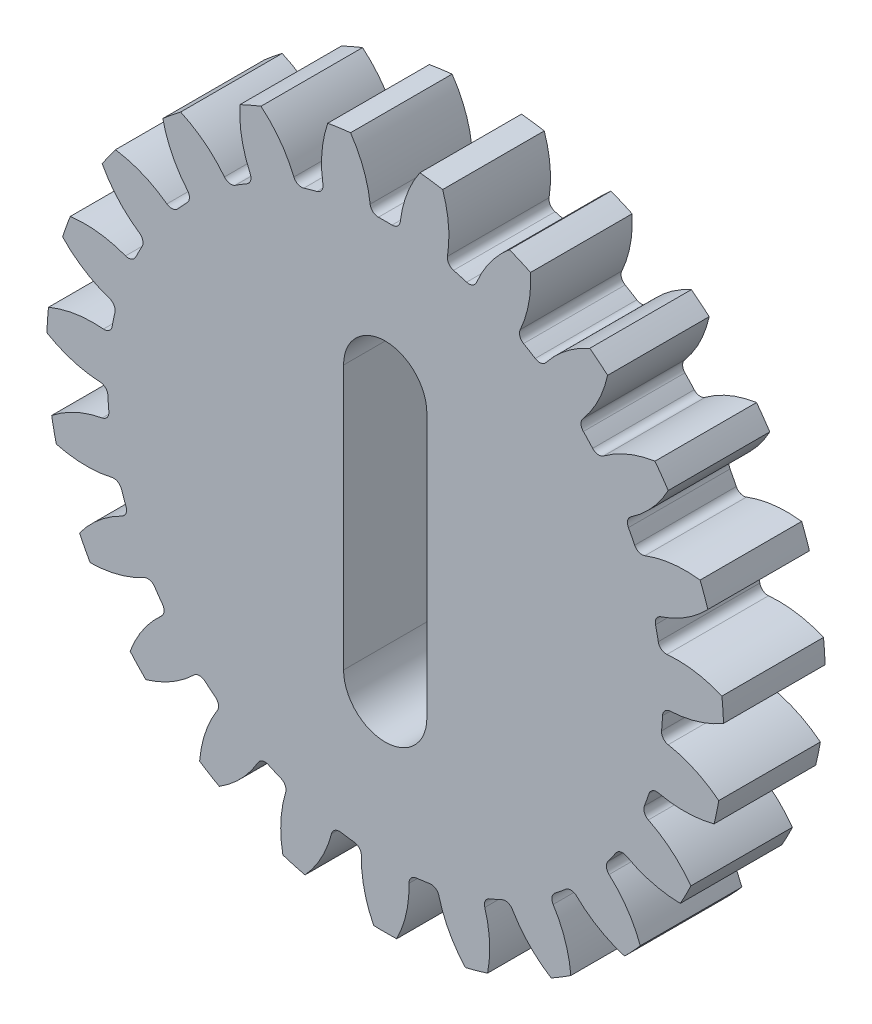
SolidWorks part; units mm, degrees
material "1023 Carbon Steel Sheet (SS)"
ref_plane "Front Plane" through (0, 0, 0) normal (0, 0, 1) x (1, 0, 0)
ref_plane "Top Plane" through (0, 0, 0) normal (0, 1, 0) x (1, 0, 0)
ref_plane "Right Plane" through (0, 0, 0) normal (1, 0, 0) x (0, 0, -1)
sketch "skBase" plane through (0, 0, 0) normal (0, 0, 1) x (1, 0, 0)
  circle A0 centre (0, 0) radius 15.3295
  circle A1 centre (0, 0) radius 16.6625
  circle A2 centre (0, 0) radius 13.6632
  dimension "D1" = 30.659
  dimension "D2" = 1.333
  dimension "D3" = 2.9992
extrude "Base" add sketch "skBase" along normal mid plane 5 contours A1
sketch "skToothProfile" plane through (0, 0, 0) normal (0, 0, 1) x (1, 0, 0)
  line L0 (0, 0) -> (0, 16.6625) construction
  line L1 (-1.0461, 15.2938) -> (1.0461, 15.2938) construction
  line L2 (-0.7109, 13.6447) -> (0, 0) construction
  line L3 (0, 12.4196) -> (-1.8721, 17.563) construction
  line L4 (0, 0) -> (2.2689, 16.5073) construction
  line L5 (1.0461, 15.2938) -> (3.1189, 15.0089) construction
  circle A0 centre (0, 0) radius 16.6625 construction
  arc A1 (-0.7109, 13.6447) -> (-2.4887, 17.4863) centre (-6.3896, 13.3489) ccw
  arc A2 (0.7109, 13.6447) -> (2.4887, 17.4863) centre (6.3896, 13.3489) cw
  circle A3 centre (0, 0) radius 13.6632 construction
  arc A4 (0.7109, 13.6447) -> (-0.7109, 13.6447) centre (0, 0) ccw
  circle A5 centre (0, 0) radius 15.3295 construction
  circle A6 centre (0, 0) radius 16.6625 construction
  circle A7 centre (0, 0) radius 17.6625
  arc A8 (2.4887, 17.4863) -> (-2.4887, 17.4863) centre (0, 0) ccw
  dimension "D2" = 20
  dimension "D3" = 7.826
  dimension "D1" = 1
extrude "ToothProfile" cut sketch "skToothProfile" against normal through all and the other way through all
fillet "FilletToothProfile" radius 0.3999 2 edges at (0.7109, 13.6447, 0) (-0.7109, 13.6447, 0)
fillet "Fillet1" [suppressed] radius 0.75
pattern_circular "CirPatternTeeth" count 23 over 360 about axis through (0, 0, 0) along (0, 0, 1) of "ToothProfile", "FilletToothProfile", "Fillet1"
sketch "skChaveta" plane through (0, 0, 2.5) normal (0, 0, 1) x (1, 0, 0)
  line L0 (0, 1.25) -> (0, 0) construction
  circle A0 centre (0, 0) radius 1.25
  dimension "D1" = 2.5
sketch "skRebaixo" plane through (0, 0, 2.5) normal (0, 0, 1) x (1, 0, 0)
  circle A0 centre (0, 0) radius 21.5
  circle A1 centre (0, 0) radius 7.5
  dimension "D1" = 43
  dimension "D2" = 15
sketch "Sketch4" plane through (0, 0, -2.5) normal (0, 0, -1) x (-1, 0, 0)
  circle A0 centre (0, 0) radius 17.5
  arc A2 (0.335, 13.6591) -> (-0.335, 13.6591) centre (0, 0) ccw
  arc A3 (0.335, 13.6591) -> (-0.335, 13.6591) centre (0, 0) ccw
  arc A63 (-1.7068, 16.5749) -> (-2.8283, 16.4207) centre (0, 0) ccw
  arc A64 (-1.7068, 16.5749) -> (-2.8283, 16.4207) centre (0, 0) ccw
  arc A67 (3.9479, -16.1881) -> (5.0379, -15.8826) centre (0, 0) ccw
  arc A68 (3.9479, -16.1881) -> (5.0379, -15.8826) centre (0, 0) ccw
  arc A69 (8.1689, -14.5226) -> (9.1362, -13.9344) centre (0, 0) ccw
  arc A70 (8.1689, -14.5226) -> (9.1362, -13.9344) centre (0, 0) ccw
  arc A71 (11.7842, -11.7802) -> (12.5569, -10.9528) centre (0, 0) ccw
  arc A72 (11.7842, -11.7802) -> (12.5569, -10.9528) centre (0, 0) ccw
  arc A73 (14.5254, -8.164) -> (15.0463, -7.1588) centre (0, 0) ccw
  arc A74 (14.5254, -8.164) -> (15.0463, -7.1588) centre (0, 0) ccw
  arc A75 (16.1894, -3.9423) -> (16.4197, -2.8339) centre (0, 0) ccw
  arc A76 (16.1894, -3.9423) -> (16.4197, -2.8339) centre (0, 0) ccw
  arc A77 (16.6527, 0.5717) -> (16.5754, 1.7011) centre (0, 0) ccw
  arc A78 (16.6527, 0.5717) -> (16.5754, 1.7011) centre (0, 0) ccw
  arc A79 (15.8809, 5.0434) -> (15.5018, 6.1101) centre (0, 0) ccw
  arc A80 (15.8809, 5.0434) -> (15.5018, 6.1101) centre (0, 0) ccw
  arc A81 (13.9313, 9.141) -> (13.2785, 10.0658) centre (0, 0) ccw
  arc A82 (13.9313, 9.141) -> (13.2785, 10.0658) centre (0, 0) ccw
  arc A83 (9.1362, -13.9344) -> (8.2674, -11.3378) centre (3.4678, -14.3873) ccw
  arc A84 (9.1362, -13.9344) -> (8.2674, -11.3378) centre (3.4678, -14.3873) ccw
  arc A85 (8.3602, -10.807) -> (8.2674, -11.3378) centre (8.6049, -11.1233) ccw
  arc A86 (8.3602, -10.807) -> (8.2674, -11.3378) centre (8.6049, -11.1233) ccw
  arc A87 (8.3602, -10.807) -> (8.88, -10.3841) centre (0, 0) ccw
  arc A88 (8.3602, -10.807) -> (8.88, -10.3841) centre (0, 0) ccw
  arc A89 (9.4186, -10.4012) -> (8.88, -10.3841) centre (9.1399, -10.688) ccw
  arc A90 (9.4186, -10.4012) -> (8.88, -10.3841) centre (9.1399, -10.688) ccw
  arc A91 (9.4186, -10.4012) -> (11.7842, -11.7802) centre (13.3808, -6.3225) ccw
  arc A92 (9.4186, -10.4012) -> (11.7842, -11.7802) centre (13.3808, -6.3225) ccw
  arc A93 (12.5569, -10.9528) -> (11.0197, -8.6868) centre (7.2209, -12.9182) ccw
  arc A94 (12.5569, -10.9528) -> (11.0197, -8.6868) centre (7.2209, -12.9182) ccw
  arc A95 (10.9659, -8.1507) -> (11.0197, -8.6868) centre (11.2868, -8.3892) ccw
  arc A96 (10.9659, -8.1507) -> (11.0197, -8.6868) centre (11.2868, -8.3892) ccw
  arc A97 (10.9659, -8.1507) -> (11.3523, -7.6032) centre (0, 0) ccw
  arc A98 (10.9659, -8.1507) -> (11.3523, -7.6032) centre (0, 0) ccw
  arc A99 (11.8755, -7.4744) -> (11.3523, -7.6032) centre (11.6846, -7.8258) ccw
  arc A100 (11.8755, -7.4744) -> (11.3523, -7.6032) centre (11.6846, -7.8258) ccw
  arc A101 (11.8755, -7.4744) -> (14.5254, -8.164) centre (14.5904, -2.4779) ccw
  arc A102 (11.8755, -7.4744) -> (14.5254, -8.164) centre (14.5904, -2.4779) ccw
  arc A103 (15.0463, -7.1588) -> (12.9547, -5.3916) centre (10.4384, -10.491) ccw
  arc A104 (15.0463, -7.1588) -> (12.9547, -5.3916) centre (10.4384, -10.491) ccw
  arc A105 (12.7583, -4.8899) -> (12.9547, -5.3916) centre (13.1317, -5.033) ccw
  arc A106 (12.7583, -4.8899) -> (12.9547, -5.3916) centre (13.1317, -5.033) ccw
  arc A107 (12.7583, -4.8899) -> (12.9827, -4.2585) centre (0, 0) ccw
  arc A108 (12.7583, -4.8899) -> (12.9827, -4.2585) centre (0, 0) ccw
  arc A109 (13.4517, -3.9933) -> (12.9827, -4.2585) centre (13.3627, -4.3831) ccw
  arc A110 (13.4517, -3.9933) -> (12.9827, -4.2585) centre (13.3627, -4.3831) ccw
  arc A111 (13.4517, -3.9933) -> (16.1894, -3.9423) centre (14.7179, 1.5504) ccw
  arc A112 (13.4517, -3.9933) -> (16.1894, -3.9423) centre (14.7179, 1.5504) ccw
  arc A113 (16.4197, -2.8339) -> (13.929, -1.6965) centre (12.8817, -7.2857) ccw
  arc A114 (16.4197, -2.8339) -> (13.929, -1.6965) centre (12.8817, -7.2857) ccw
  arc A115 (13.6044, -1.2664) -> (13.929, -1.6965) centre (14.0026, -1.3035) ccw
  arc A116 (13.6044, -1.2664) -> (13.929, -1.6965) centre (14.0026, -1.3035) ccw
  arc A117 (13.6044, -1.2664) -> (13.6502, -0.5979) centre (0, 0) ccw
  arc A118 (13.6044, -1.2664) -> (13.6502, -0.5979) centre (0, 0) ccw
  arc A119 (14.0302, -0.2159) -> (13.6502, -0.5979) centre (14.0497, -0.6154) ccw
  arc A120 (14.0302, -0.2159) -> (13.6502, -0.5979) centre (14.0497, -0.6154) ccw
  arc A121 (14.0302, -0.2159) -> (16.6527, 0.5717) centre (13.7538, 5.4638) ccw
  arc A122 (14.0302, -0.2159) -> (16.6527, 0.5717) centre (13.7538, 5.4638) ccw
  arc A123 (16.5754, 1.7011) -> (13.8702, 2.1244) centre (14.3697, -3.5401) ccw
  arc A124 (16.5754, 1.7011) -> (13.8702, 2.1244) centre (14.3697, -3.5401) ccw
  arc A125 (13.4416, 2.451) -> (13.8702, 2.1244) centre (13.835, 2.5227) ccw
  arc A126 (13.4416, 2.451) -> (13.8702, 2.1244) centre (13.835, 2.5227) ccw
  arc A127 (13.4416, 2.451) -> (13.3053, 3.1071) centre (0, 0) ccw
  arc A128 (13.4416, 2.451) -> (13.3053, 3.1071) centre (0, 0) ccw
  arc A129 (13.5682, 3.5774) -> (13.3053, 3.1071) centre (13.6947, 3.198) ccw
  arc A130 (13.5682, 3.5774) -> (13.3053, 3.1071) centre (13.6947, 3.198) ccw
  arc A131 (13.5682, 3.5774) -> (15.8809, 5.0434) centre (11.7697, 8.9719) ccw
  arc A132 (13.5682, 3.5774) -> (15.8809, 5.0434) centre (11.7697, 8.9719) ccw
  arc A133 (15.5018, 6.1101) -> (12.7827, 5.7877) centre (14.7919, 0.4681) ccw
  arc A134 (15.5018, 6.1101) -> (12.7827, 5.7877) centre (14.7919, 0.4681) ccw
  arc A135 (12.2819, 5.9866) -> (12.7827, 5.7877) centre (12.6414, 6.1618) ccw
  arc A136 (12.2819, 5.9866) -> (12.7827, 5.7877) centre (12.6414, 6.1618) ccw
  arc A137 (12.2819, 5.9866) -> (11.9736, 6.5816) centre (0, 0) ccw
  arc A138 (12.2819, 5.9866) -> (11.9736, 6.5816) centre (0, 0) ccw
  arc A139 (12.0999, 7.1054) -> (11.9736, 6.5816) centre (12.3241, 6.7742) ccw
  arc A140 (12.0999, 7.1054) -> (11.9736, 6.5816) centre (12.3241, 6.7742) ccw
  arc A141 (12.0999, 7.1054) -> (13.9313, 9.141) centre (8.9126, 11.8146) ccw
  arc A142 (12.0999, 7.1054) -> (13.9313, 9.141) centre (8.9126, 11.8146) ccw
  arc A143 (13.2785, 10.0658) -> (10.7471, 9.0218) centre (14.1171, 4.4415) ccw
  arc A144 (13.2785, 10.0658) -> (10.7471, 9.0218) centre (14.1171, 4.4415) ccw
  arc A145 (10.2113, 9.0782) -> (10.7471, 9.0218) centre (10.5101, 9.3439) ccw
  arc A146 (10.2113, 9.0782) -> (10.7471, 9.0218) centre (10.5101, 9.3439) ccw
  arc A147 (10.2113, 9.0782) -> (9.7539, 9.5679) centre (0, 0) ccw
  arc A148 (10.2113, 9.0782) -> (9.7539, 9.5679) centre (0, 0) ccw
  arc A149 (9.7342, 10.1064) -> (9.7539, 9.5679) centre (10.0394, 9.848) ccw
  arc A150 (9.7342, 10.1064) -> (9.7539, 9.5679) centre (10.0394, 9.848) ccw
  arc A151 (9.7342, 10.1064) -> (10.9485, 12.5606) centre (5.3946, 13.7811) ccw
  arc A152 (9.7342, 10.1064) -> (10.9485, 12.5606) centre (5.3946, 13.7811) ccw
  arc A153 (10.0704, 13.275) -> (7.9145, 11.5868) centre (12.3953, 8.0856) ccw
  arc A154 (10.0704, 13.275) -> (7.9145, 11.5868) centre (12.3953, 8.0856) ccw
  arc A155 (7.3833, 11.4966) -> (7.9145, 11.5868) centre (7.5994, 11.833) ccw
  arc A156 (7.3833, 11.4966) -> (7.9145, 11.5868) centre (7.5994, 11.833) ccw
  arc A157 (7.3833, 11.4966) -> (6.8108, 11.8447) centre (0, 0) ccw
  arc A158 (7.3833, 11.4966) -> (6.8108, 11.8447) centre (0, 0) ccw
  arc A159 (6.6466, 12.3579) -> (6.8108, 11.8447) centre (7.0101, 12.1914) ccw
  arc A160 (6.6466, 12.3579) -> (6.8108, 11.8447) centre (7.0101, 12.1914) ccw
  arc A161 (6.6466, 12.3579) -> (7.1537, 15.0487) centre (1.4764, 14.7255) ccw
  arc A162 (6.6466, 12.3579) -> (7.1537, 15.0487) centre (1.4764, 14.7255) ccw
  arc A163 (6.1154, 15.4997) -> (4.495, 13.2925) centre (9.7542, 11.13) ccw
  arc A164 (6.1154, 15.4997) -> (4.495, 13.2925) centre (9.7542, 11.13) ccw
  arc A165 (4.0078, 13.0622) -> (4.495, 13.2925) centre (4.1251, 13.4445) ccw
  arc A166 (4.0078, 13.0622) -> (4.495, 13.2925) centre (4.1251, 13.4445) ccw
  arc A167 (4.0078, 13.0622) -> (3.3626, 13.243) centre (0, 0) ccw
  arc A168 (4.0078, 13.0622) -> (3.3626, 13.243) centre (0, 0) ccw
  arc A169 (3.066, 13.6928) -> (3.3626, 13.243) centre (3.461, 13.6306) ccw
  arc A170 (3.066, 13.6928) -> (3.3626, 13.243) centre (3.461, 13.6306) ccw
  arc A171 (3.066, 13.6928) -> (2.8283, 16.4207) centre (-2.5512, 14.5778) ccw
  arc A172 (3.066, 13.6928) -> (2.8283, 16.4207) centre (-2.5512, 14.5778) ccw
  arc A173 (1.7068, 16.5749) -> (0.742, 14.0123) centre (6.3896, 13.3489) ccw
  arc A174 (1.7068, 16.5749) -> (0.742, 14.0123) centre (6.3896, 13.3489) ccw
  arc A175 (0.335, 13.6591) -> (0.742, 14.0123) centre (0.3448, 14.0589) ccw
  arc A176 (0.335, 13.6591) -> (0.742, 14.0123) centre (0.3448, 14.0589) ccw
  arc A177 (-0.742, 14.0123) -> (-0.335, 13.6591) centre (-0.3448, 14.0589) ccw
  arc A178 (-0.742, 14.0123) -> (-0.335, 13.6591) centre (-0.3448, 14.0589) ccw
  arc A179 (-0.742, 14.0123) -> (-1.7068, 16.5749) centre (-6.3896, 13.3489) ccw
  arc A180 (-0.742, 14.0123) -> (-1.7068, 16.5749) centre (-6.3896, 13.3489) ccw
  arc A199 (10.9485, 12.5606) -> (10.0704, 13.275) centre (0, 0) ccw
  arc A200 (10.9485, 12.5606) -> (10.0704, 13.275) centre (0, 0) ccw
  arc A201 (7.1537, 15.0487) -> (6.1154, 15.4997) centre (0, 0) ccw
  arc A202 (7.1537, 15.0487) -> (6.1154, 15.4997) centre (0, 0) ccw
  arc A203 (2.8283, 16.4207) -> (1.7068, 16.5749) centre (0, 0) ccw
  arc A204 (2.8283, 16.4207) -> (1.7068, 16.5749) centre (0, 0) ccw
  arc A215 (-9.1362, -13.9344) -> (-8.1689, -14.5226) centre (0, 0) ccw
  arc A216 (-9.1362, -13.9344) -> (-8.1689, -14.5226) centre (0, 0) ccw
  arc A217 (-5.0379, -15.8826) -> (-3.9479, -16.1881) centre (0, 0) ccw
  arc A218 (-5.0379, -15.8826) -> (-3.9479, -16.1881) centre (0, 0) ccw
  arc A219 (-0.566, -16.6529) -> (0.566, -16.6529) centre (0, 0) ccw
  arc A220 (-0.566, -16.6529) -> (0.566, -16.6529) centre (0, 0) ccw
  arc A221 (-1.1729, -13.9828) -> (-0.566, -16.6529) centre (4.5125, -14.0946) ccw
  arc A222 (-1.1729, -13.9828) -> (-0.566, -16.6529) centre (4.5125, -14.0946) ccw
  arc A223 (-3.9479, -16.1881) -> (-2.6431, -13.7807) centre (-8.1478, -12.3545) ccw
  arc A224 (-3.9479, -16.1881) -> (-2.6431, -13.7807) centre (-8.1478, -12.3545) ccw
  arc A225 (-2.1918, -13.4863) -> (-2.6431, -13.7807) centre (-2.256, -13.881) ccw
  arc A226 (-2.1918, -13.4863) -> (-2.6431, -13.7807) centre (-2.256, -13.881) ccw
  arc A227 (-2.1918, -13.4863) -> (-1.528, -13.5775) centre (0, 0) ccw
  arc A228 (-2.1918, -13.4863) -> (-1.528, -13.5775) centre (0, 0) ccw
  arc A229 (-1.1729, -13.9828) -> (-1.528, -13.5775) centre (-1.5727, -13.9749) ccw
  arc A230 (-1.1729, -13.9828) -> (-1.528, -13.5775) centre (-1.5727, -13.9749) ccw
  arc A231 (-11.7842, -11.7802) -> (-9.4186, -10.4012) centre (-13.3808, -6.3225) ccw
  arc A232 (-11.7842, -11.7802) -> (-9.4186, -10.4012) centre (-13.3808, -6.3225) ccw
  arc A233 (-8.88, -10.3841) -> (-9.4186, -10.4012) centre (-9.1399, -10.688) ccw
  arc A234 (-8.88, -10.3841) -> (-9.4186, -10.4012) centre (-9.1399, -10.688) ccw
  arc A235 (-8.88, -10.3841) -> (-8.3602, -10.807) centre (0, 0) ccw
  arc A236 (-8.88, -10.3841) -> (-8.3602, -10.807) centre (0, 0) ccw
  arc A237 (-8.2674, -11.3378) -> (-8.3602, -10.807) centre (-8.6049, -11.1233) ccw
  arc A238 (-8.2674, -11.3378) -> (-8.3602, -10.807) centre (-8.6049, -11.1233) ccw
  arc A239 (-8.2674, -11.3378) -> (-9.1362, -13.9344) centre (-3.4678, -14.3873) ccw
  arc A240 (-8.2674, -11.3378) -> (-9.1362, -13.9344) centre (-3.4678, -14.3873) ccw
  arc A241 (-8.1689, -14.5226) -> (-6.2631, -12.5566) centre (-11.1789, -9.6981) ccw
  arc A242 (-8.1689, -14.5226) -> (-6.2631, -12.5566) centre (-11.1789, -9.6981) ccw
  arc A243 (-5.7491, -12.3948) -> (-6.2631, -12.5566) centre (-5.9174, -12.7576) ccw
  arc A244 (-5.7491, -12.3948) -> (-6.2631, -12.5566) centre (-5.9174, -12.7576) ccw
  arc A245 (-5.7491, -12.3948) -> (-5.1345, -12.6618) centre (0, 0) ccw
  arc A246 (-5.7491, -12.3948) -> (-5.1345, -12.6618) centre (0, 0) ccw
  arc A247 (-4.9019, -13.1478) -> (-5.1345, -12.6618) centre (-5.2848, -13.0324) ccw
  arc A248 (-4.9019, -13.1478) -> (-5.1345, -12.6618) centre (-5.2848, -13.0324) ccw
  arc A249 (-4.9019, -13.1478) -> (-5.0379, -15.8826) centre (0.5424, -14.7894) ccw
  arc A250 (-4.9019, -13.1478) -> (-5.0379, -15.8826) centre (0.5424, -14.7894) ccw
  arc A273 (0.566, -16.6529) -> (1.1729, -13.9828) centre (-4.5125, -14.0946) ccw
  arc A274 (0.566, -16.6529) -> (1.1729, -13.9828) centre (-4.5125, -14.0946) ccw
  arc A275 (1.528, -13.5775) -> (1.1729, -13.9828) centre (1.5727, -13.9749) ccw
  arc A276 (1.528, -13.5775) -> (1.1729, -13.9828) centre (1.5727, -13.9749) ccw
  arc A277 (1.528, -13.5775) -> (2.1918, -13.4863) centre (0, 0) ccw
  arc A278 (1.528, -13.5775) -> (2.1918, -13.4863) centre (0, 0) ccw
  arc A279 (2.6431, -13.7807) -> (2.1918, -13.4863) centre (2.256, -13.881) ccw
  arc A280 (2.6431, -13.7807) -> (2.1918, -13.4863) centre (2.256, -13.881) ccw
  arc A281 (2.6431, -13.7807) -> (3.9479, -16.1881) centre (8.1478, -12.3545) ccw
  arc A282 (2.6431, -13.7807) -> (3.9479, -16.1881) centre (8.1478, -12.3545) ccw
  arc A289 (5.0379, -15.8826) -> (4.9019, -13.1478) centre (-0.5424, -14.7894) ccw
  arc A290 (5.0379, -15.8826) -> (4.9019, -13.1478) centre (-0.5424, -14.7894) ccw
  arc A291 (5.1345, -12.6618) -> (4.9019, -13.1478) centre (5.2848, -13.0324) ccw
  arc A292 (5.1345, -12.6618) -> (4.9019, -13.1478) centre (5.2848, -13.0324) ccw
  arc A293 (5.1345, -12.6618) -> (5.7491, -12.3948) centre (0, 0) ccw
  arc A294 (5.1345, -12.6618) -> (5.7491, -12.3948) centre (0, 0) ccw
  arc A295 (6.2631, -12.5566) -> (5.7491, -12.3948) centre (5.9174, -12.7576) ccw
  arc A296 (6.2631, -12.5566) -> (5.7491, -12.3948) centre (5.9174, -12.7576) ccw
  arc A297 (6.2631, -12.5566) -> (8.1689, -14.5226) centre (11.1789, -9.6981) ccw
  arc A298 (6.2631, -12.5566) -> (8.1689, -14.5226) centre (11.1789, -9.6981) ccw
  arc A319 (-12.5569, -10.9528) -> (-11.7842, -11.7802) centre (0, 0) ccw
  arc A320 (-12.5569, -10.9528) -> (-11.7842, -11.7802) centre (0, 0) ccw
  arc A321 (-15.5018, 6.1101) -> (-15.8809, 5.0434) centre (0, 0) ccw
  arc A322 (-15.5018, 6.1101) -> (-15.8809, 5.0434) centre (0, 0) ccw
  arc A323 (-16.5754, 1.7011) -> (-16.6527, 0.5717) centre (0, 0) ccw
  arc A324 (-16.5754, 1.7011) -> (-16.6527, 0.5717) centre (0, 0) ccw
  arc A325 (-16.4197, -2.8339) -> (-16.1894, -3.9423) centre (0, 0) ccw
  arc A326 (-16.4197, -2.8339) -> (-16.1894, -3.9423) centre (0, 0) ccw
  arc A327 (-15.0463, -7.1588) -> (-14.5254, -8.164) centre (0, 0) ccw
  arc A328 (-15.0463, -7.1588) -> (-14.5254, -8.164) centre (0, 0) ccw
  arc A329 (-2.8283, 16.4207) -> (-3.066, 13.6928) centre (2.5512, 14.5778) ccw
  arc A330 (-2.8283, 16.4207) -> (-3.066, 13.6928) centre (2.5512, 14.5778) ccw
  arc A331 (-3.3626, 13.243) -> (-3.066, 13.6928) centre (-3.461, 13.6306) ccw
  arc A332 (-3.3626, 13.243) -> (-3.066, 13.6928) centre (-3.461, 13.6306) ccw
  arc A333 (-3.3626, 13.243) -> (-4.0078, 13.0622) centre (0, 0) ccw
  arc A334 (-3.3626, 13.243) -> (-4.0078, 13.0622) centre (0, 0) ccw
  arc A335 (-4.495, 13.2925) -> (-4.0078, 13.0622) centre (-4.1251, 13.4445) ccw
  arc A336 (-4.495, 13.2925) -> (-4.0078, 13.0622) centre (-4.1251, 13.4445) ccw
  arc A337 (-4.495, 13.2925) -> (-6.1154, 15.4997) centre (-9.7542, 11.13) ccw
  arc A338 (-4.495, 13.2925) -> (-6.1154, 15.4997) centre (-9.7542, 11.13) ccw
  arc A339 (-6.1154, 15.4997) -> (-7.1537, 15.0487) centre (0, 0) ccw
  arc A340 (-6.1154, 15.4997) -> (-7.1537, 15.0487) centre (0, 0) ccw
  arc A341 (-7.1537, 15.0487) -> (-6.6466, 12.3579) centre (-1.4764, 14.7255) ccw
  arc A342 (-7.1537, 15.0487) -> (-6.6466, 12.3579) centre (-1.4764, 14.7255) ccw
  arc A343 (-6.8108, 11.8447) -> (-6.6466, 12.3579) centre (-7.0101, 12.1914) ccw
  arc A344 (-6.8108, 11.8447) -> (-6.6466, 12.3579) centre (-7.0101, 12.1914) ccw
  arc A345 (-6.8108, 11.8447) -> (-7.3833, 11.4966) centre (0, 0) ccw
  arc A346 (-6.8108, 11.8447) -> (-7.3833, 11.4966) centre (0, 0) ccw
  arc A347 (-7.9145, 11.5868) -> (-7.3833, 11.4966) centre (-7.5994, 11.833) ccw
  arc A348 (-7.9145, 11.5868) -> (-7.3833, 11.4966) centre (-7.5994, 11.833) ccw
  arc A349 (-7.9145, 11.5868) -> (-10.0704, 13.275) centre (-12.3953, 8.0856) ccw
  arc A350 (-7.9145, 11.5868) -> (-10.0704, 13.275) centre (-12.3953, 8.0856) ccw
  arc A351 (-10.0704, 13.275) -> (-10.9485, 12.5606) centre (0, 0) ccw
  arc A352 (-10.0704, 13.275) -> (-10.9485, 12.5606) centre (0, 0) ccw
  arc A353 (-10.9485, 12.5606) -> (-9.7342, 10.1064) centre (-5.3946, 13.7811) ccw
  arc A354 (-10.9485, 12.5606) -> (-9.7342, 10.1064) centre (-5.3946, 13.7811) ccw
  arc A355 (-9.7539, 9.5679) -> (-9.7342, 10.1064) centre (-10.0394, 9.848) ccw
  arc A356 (-9.7539, 9.5679) -> (-9.7342, 10.1064) centre (-10.0394, 9.848) ccw
  arc A357 (-9.7539, 9.5679) -> (-10.2113, 9.0782) centre (0, 0) ccw
  arc A358 (-9.7539, 9.5679) -> (-10.2113, 9.0782) centre (0, 0) ccw
  arc A359 (-10.7471, 9.0218) -> (-10.2113, 9.0782) centre (-10.5101, 9.3439) ccw
  arc A360 (-10.7471, 9.0218) -> (-10.2113, 9.0782) centre (-10.5101, 9.3439) ccw
  arc A361 (-10.7471, 9.0218) -> (-13.2785, 10.0658) centre (-14.1171, 4.4415) ccw
  arc A362 (-10.7471, 9.0218) -> (-13.2785, 10.0658) centre (-14.1171, 4.4415) ccw
  arc A363 (-13.2785, 10.0658) -> (-13.9313, 9.141) centre (0, 0) ccw
  arc A364 (-13.2785, 10.0658) -> (-13.9313, 9.141) centre (0, 0) ccw
  arc A365 (-13.9313, 9.141) -> (-12.0999, 7.1054) centre (-8.9126, 11.8146) ccw
  arc A366 (-13.9313, 9.141) -> (-12.0999, 7.1054) centre (-8.9126, 11.8146) ccw
  arc A367 (-11.9736, 6.5816) -> (-12.0999, 7.1054) centre (-12.3241, 6.7742) ccw
  arc A368 (-11.9736, 6.5816) -> (-12.0999, 7.1054) centre (-12.3241, 6.7742) ccw
  arc A369 (-11.9736, 6.5816) -> (-12.2819, 5.9866) centre (0, 0) ccw
  arc A370 (-11.9736, 6.5816) -> (-12.2819, 5.9866) centre (0, 0) ccw
  arc A371 (-12.7827, 5.7877) -> (-12.2819, 5.9866) centre (-12.6414, 6.1618) ccw
  arc A372 (-12.7827, 5.7877) -> (-12.2819, 5.9866) centre (-12.6414, 6.1618) ccw
  arc A373 (-12.7827, 5.7877) -> (-15.5018, 6.1101) centre (-14.7919, 0.4681) ccw
  arc A374 (-12.7827, 5.7877) -> (-15.5018, 6.1101) centre (-14.7919, 0.4681) ccw
  arc A375 (-15.8809, 5.0434) -> (-13.5682, 3.5774) centre (-11.7697, 8.9719) ccw
  arc A376 (-15.8809, 5.0434) -> (-13.5682, 3.5774) centre (-11.7697, 8.9719) ccw
  arc A377 (-13.3053, 3.1071) -> (-13.5682, 3.5774) centre (-13.6947, 3.198) ccw
  arc A378 (-13.3053, 3.1071) -> (-13.5682, 3.5774) centre (-13.6947, 3.198) ccw
  arc A379 (-13.3053, 3.1071) -> (-13.4416, 2.451) centre (0, 0) ccw
  arc A380 (-13.3053, 3.1071) -> (-13.4416, 2.451) centre (0, 0) ccw
  arc A381 (-13.8702, 2.1244) -> (-13.4416, 2.451) centre (-13.835, 2.5227) ccw
  arc A382 (-13.8702, 2.1244) -> (-13.4416, 2.451) centre (-13.835, 2.5227) ccw
  arc A383 (-13.8702, 2.1244) -> (-16.5754, 1.7011) centre (-14.3697, -3.5401) ccw
  arc A384 (-13.8702, 2.1244) -> (-16.5754, 1.7011) centre (-14.3697, -3.5401) ccw
  arc A385 (-16.6527, 0.5717) -> (-14.0302, -0.2159) centre (-13.7538, 5.4638) ccw
  arc A386 (-16.6527, 0.5717) -> (-14.0302, -0.2159) centre (-13.7538, 5.4638) ccw
  arc A387 (-13.6502, -0.5979) -> (-14.0302, -0.2159) centre (-14.0497, -0.6154) ccw
  arc A388 (-13.6502, -0.5979) -> (-14.0302, -0.2159) centre (-14.0497, -0.6154) ccw
  arc A389 (-13.6502, -0.5979) -> (-13.6044, -1.2664) centre (0, 0) ccw
  arc A390 (-13.6502, -0.5979) -> (-13.6044, -1.2664) centre (0, 0) ccw
  arc A391 (-13.929, -1.6965) -> (-13.6044, -1.2664) centre (-14.0026, -1.3035) ccw
  arc A392 (-13.929, -1.6965) -> (-13.6044, -1.2664) centre (-14.0026, -1.3035) ccw
  arc A393 (-13.929, -1.6965) -> (-16.4197, -2.8339) centre (-12.8817, -7.2857) ccw
  arc A394 (-13.929, -1.6965) -> (-16.4197, -2.8339) centre (-12.8817, -7.2857) ccw
  arc A395 (-16.1894, -3.9423) -> (-13.4517, -3.9933) centre (-14.7179, 1.5504) ccw
  arc A396 (-16.1894, -3.9423) -> (-13.4517, -3.9933) centre (-14.7179, 1.5504) ccw
  arc A397 (-12.9827, -4.2585) -> (-13.4517, -3.9933) centre (-13.3627, -4.3831) ccw
  arc A398 (-12.9827, -4.2585) -> (-13.4517, -3.9933) centre (-13.3627, -4.3831) ccw
  arc A399 (-12.9827, -4.2585) -> (-12.7583, -4.8899) centre (0, 0) ccw
  arc A400 (-12.9827, -4.2585) -> (-12.7583, -4.8899) centre (0, 0) ccw
  arc A401 (-12.9547, -5.3916) -> (-12.7583, -4.8899) centre (-13.1317, -5.033) ccw
  arc A402 (-12.9547, -5.3916) -> (-12.7583, -4.8899) centre (-13.1317, -5.033) ccw
  arc A403 (-12.9547, -5.3916) -> (-15.0463, -7.1588) centre (-10.4384, -10.491) ccw
  arc A404 (-12.9547, -5.3916) -> (-15.0463, -7.1588) centre (-10.4384, -10.491) ccw
  arc A405 (-14.5254, -8.164) -> (-11.8755, -7.4744) centre (-14.5904, -2.4779) ccw
  arc A406 (-14.5254, -8.164) -> (-11.8755, -7.4744) centre (-14.5904, -2.4779) ccw
  arc A407 (-11.3523, -7.6032) -> (-11.8755, -7.4744) centre (-11.6846, -7.8258) ccw
  arc A408 (-11.3523, -7.6032) -> (-11.8755, -7.4744) centre (-11.6846, -7.8258) ccw
  arc A409 (-11.3523, -7.6032) -> (-10.9659, -8.1507) centre (0, 0) ccw
  arc A410 (-11.3523, -7.6032) -> (-10.9659, -8.1507) centre (0, 0) ccw
  arc A411 (-11.0197, -8.6868) -> (-10.9659, -8.1507) centre (-11.2868, -8.3892) ccw
  arc A412 (-11.0197, -8.6868) -> (-10.9659, -8.1507) centre (-11.2868, -8.3892) ccw
  arc A413 (-11.0197, -8.6868) -> (-12.5569, -10.9528) centre (-7.2209, -12.9182) ccw
  arc A414 (-11.0197, -8.6868) -> (-12.5569, -10.9528) centre (-7.2209, -12.9182) ccw
  dimension "D1" = 0
sketch "Sketch5" plane through (0, 0, -2.5) normal (0, 0, -1) x (-1, 0, 0)
  line L0 (0, 6.5) -> (0, -6.5) construction
  line L1 (2.05, 6.5) -> (2.05, -6.5)
  line L2 (-2.05, 6.5) -> (-2.05, -6.5)
  arc A0 (2.05, 6.5) -> (-2.05, 6.5) centre (0, 6.5) ccw
  arc A1 (-2.05, -6.5) -> (2.05, -6.5) centre (0, -6.5) ccw
  point P3 (0, 0)
  dimension "D1" = 2.05
  dimension "D2" = 13
extrude "Cut-Extrude1" cut sketch "Sketch5" against normal through all
equation "\"Module\"= 1.333mm"
equation "\"Number_Of_Teeth\"= 23"
equation "\"D1@skBase\"=\"Module\" * \"Number_Of_Teeth\""
equation "\"D2@skBase\"=\"Module\""
equation "\"D3@skBase\"=\"Module\" * if( \"Module\" >=1.25, 2.25, 2.4)"
equation "\"Pressure_Angle\"= 20deg"
equation "\"D2@skToothProfile\"=\"Pressure_Angle\""
equation "\"D3@skToothProfile\"=180 / \"Number_Of_Teeth\""
equation "\"D1@FilletToothProfile\"= 0.3 * \"Module\""
equation "\"D1@CirPatternTeeth\"=\"Number_Of_Teeth\""
equation "\"Width\" = 5mm"
equation "\"D1@Base\"=\"Width\""
